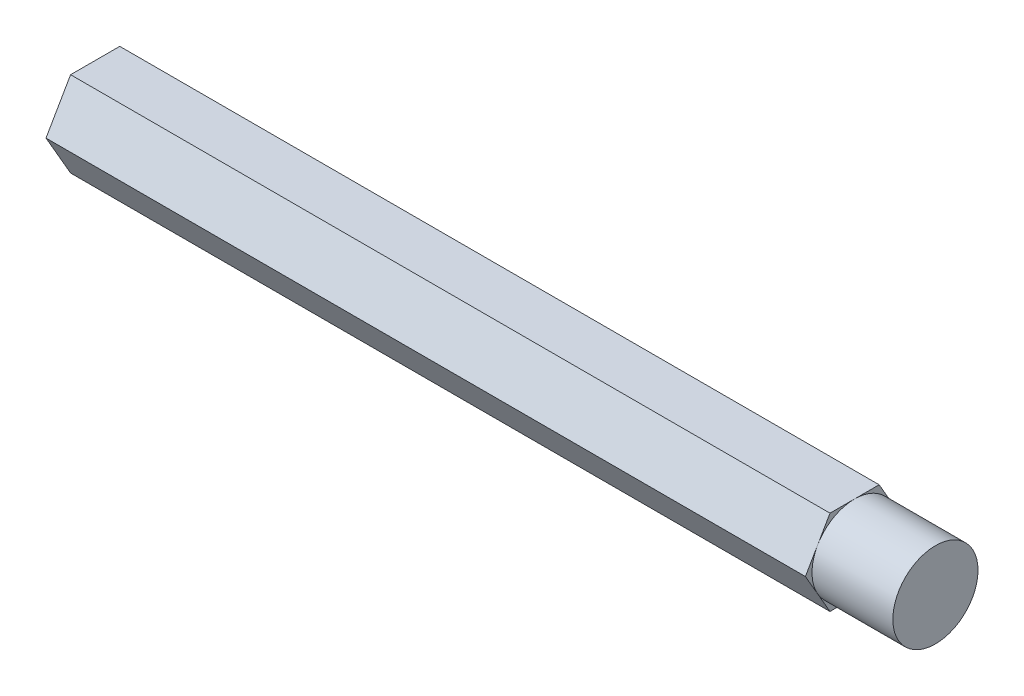
SolidWorks part; units mm, degrees
material "7075-T6 (SN)"
ref_plane "Front Plane" through (0, 0, 0) normal (0, 0, 1) x (1, 0, 0)
ref_plane "Top Plane" through (0, 0, 0) normal (0, 1, 0) x (1, 0, 0)
ref_plane "Right Plane" through (0, 0, 0) normal (1, 0, 0) x (0, 0, -1)
sketch "Sketch1" plane through (0, 0, 0) normal (1, 0, 0) x (0, 0, -1)
  line L1 (-5.4993, 0) -> (-2.7496, -4.7625)
  line L2 (-2.7496, -4.7625) -> (2.7496, -4.7625)
  line L3 (2.7496, -4.7625) -> (5.4993, 0)
  line L4 (5.4993, 0) -> (2.7496, 4.7625)
  line L5 (2.7496, 4.7625) -> (-2.7496, 4.7625)
  line L6 (-2.7496, 4.7625) -> (-5.4993, 0)
  circle A1 centre (0, 0) radius 4.7625 construction
  dimension "D1" = 9.525
extrude "Boss-Extrude1" add sketch "Sketch1" along normal blind 93.98
sketch "Sketch2" plane through (93.98, 0, 0) normal (1, 0, 0) x (0, 0, -1)
  circle A0 centre (0, 0) radius 4.7625
  circle A1 centre (0, 0) radius 5.4993
  dimension "D1" = 9.525
extrude "Cut-Extrude1" cut sketch "Sketch2" against normal blind 9.0424
pattern_linear "LPattern1" [suppressed] count 2 spacing 38.1
